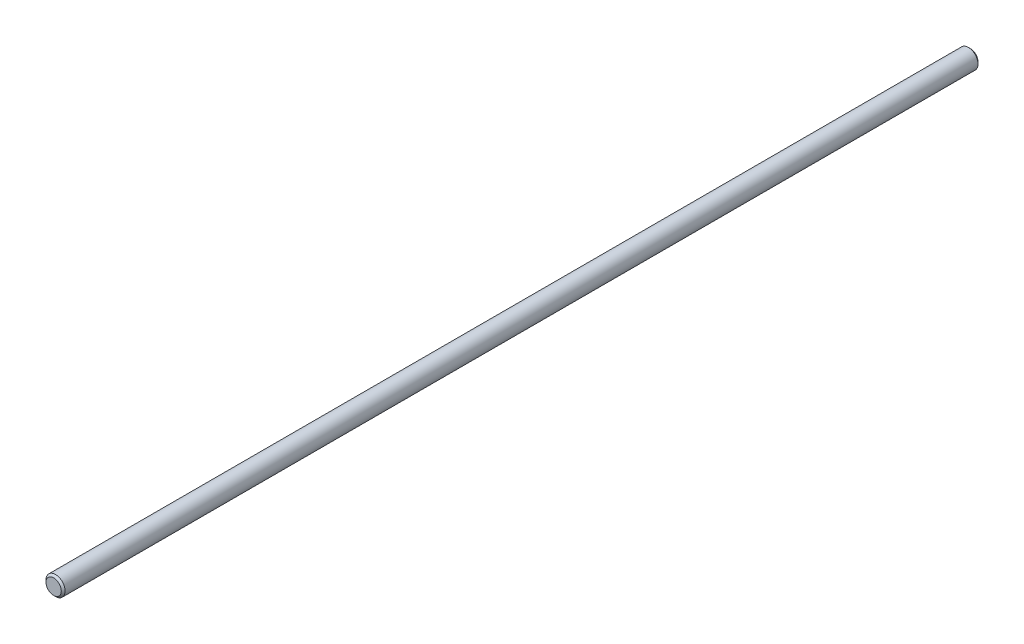
SolidWorks part; units mm, degrees
ref_plane "Front" through (0, 0, 0) normal (0, 0, 1) x (1, 0, 0)
ref_plane "Top" through (0, 0, 0) normal (0, 1, 0) x (1, 0, 0)
ref_plane "Right" through (0, 0, 0) normal (1, 0, 0) x (0, 0, -1)
sketch "Sketch1" plane through (0, 0, 0) normal (0, 0, 1) x (1, 0, 0)
  circle A0 centre (0, 0) radius 6.35
  dimension "dia" = 12.7
extrude "Extrude1" add sketch "Sketch1" along normal mid plane 609.6
sketch "Sketch2" plane through (0, 0, 0) normal (1, 0, 0) x (0, 0, -1)
  point P0 (-304.8, 6.35)
  point P1 (304.8, 6.35)
chamfer "Chamfer1" distance 1.27 angle 45 2 edges at (6.35, 0, -304.8) (6.35, 0, 304.8)
equation "\"D1@Chamfer1\" = \"dia@Sketch1\" * .1"
